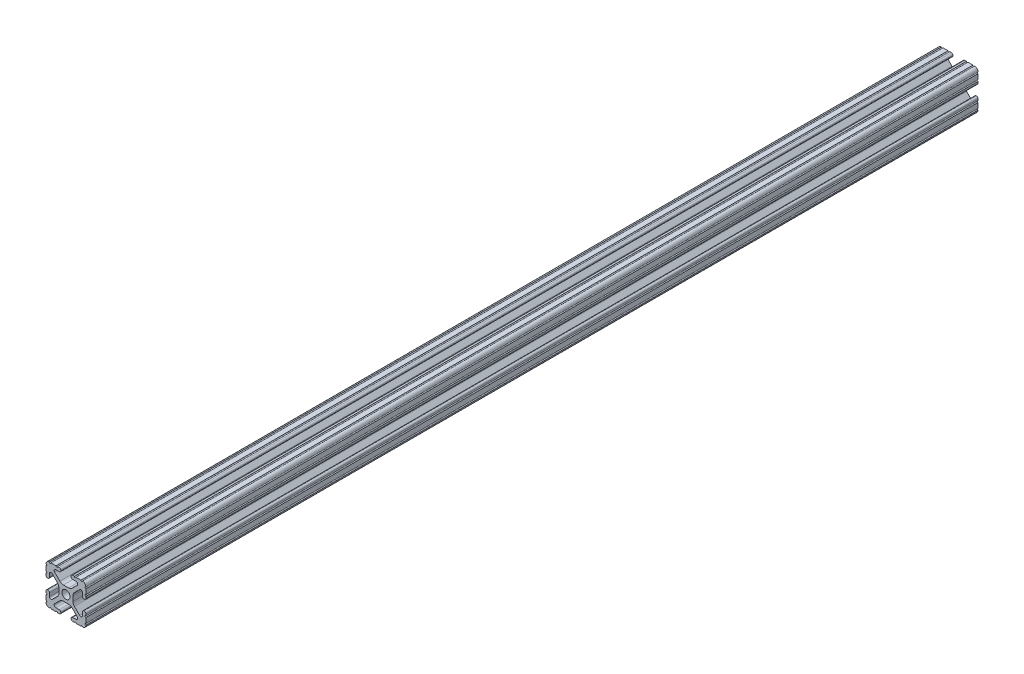
SolidWorks part; units mm, degrees
material "6061 Alloy"
ref_plane "Front" through (0, 0, 0) normal (0, 0, 1) x (1, 0, 0)
ref_plane "Top" through (0, 0, 0) normal (0, 1, 0) x (1, 0, 0)
ref_plane "Right" through (0, 0, 0) normal (1, 0, 0) x (0, 0, -1)
sketch "Sketch1" plane through (0, 0, 0) normal (0, 0, 1) x (1, 0, 0)
  line L0 (-3.2512, 12.7) -> (-3.2512, -12.7) construction
  line L1 (-12.7, -12.7) -> (12.7, -12.7) construction
  line L2 (-12.7, -12.7) -> (-12.7, 12.7) construction
  line L3 (-12.7, 12.7) -> (12.7, 12.7) construction
  line L4 (12.7, -12.7) -> (12.7, 12.7) construction
  line L5 (0, 12.7) -> (0, -12.7) construction
  line L6 (-12.7, 0) -> (12.7, 0) construction
  line L7 (3.2512, 12.7) -> (3.2512, -12.7) construction
  line L8 (-3.2512, 12.7) -> (3.2512, -12.7) construction
  circle A0 centre (0, 0) radius 2.6035
  point P0 (0, 0)
  line B0 (-7.5107, 9.4563) -> (7.5107, 9.4563) construction
  line B1 (-7.4968, -9.4098) -> (7.4968, -9.4098) construction
  line B2 (-7.1797, -8.6452) -> (-3.9523, -5.4237)
  line B3 (-1.7093, -4.4958) -> (1.7093, -4.4958)
  line B4 (3.9523, -5.4237) -> (7.1797, -8.6452)
  line B5 (6.4164, -10.4902) -> (4.2875, -10.4902)
  line B6 (3.2385, -11.5392) -> (3.2385, -11.651)
  line B7 (4.2875, -12.7) -> (5.3171, -12.7)
  line B8 (6.3331, -12.7) -> (9.5504, -12.7)
  line B9 (12.7, -9.5504) -> (12.7, -6.3331)
  line B10 (12.7, -5.3171) -> (12.7, -4.2875)
  line B11 (11.651, -3.2385) -> (11.5392, -3.2385)
  line B12 (10.4902, -4.2875) -> (10.4902, -6.4021)
  line B13 (8.7371, -7.1294) -> (5.441, -3.8408)
  line B14 (4.5085, -1.5932) -> (4.5085, 1.5932)
  line B15 (5.441, 3.8408) -> (8.7371, 7.1294)
  line B16 (10.4902, 6.4021) -> (10.4902, 4.2875)
  line B17 (11.5392, 3.2385) -> (11.651, 3.2385)
  line B18 (12.7, 4.2875) -> (12.7, 5.3171)
  line B19 (12.7, 6.3331) -> (12.7, 9.5504)
  line B20 (9.5504, 12.7) -> (6.3331, 12.7)
  line B21 (5.3171, 12.7) -> (4.2875, 12.7)
  line B22 (3.2385, 11.651) -> (3.2385, 11.5392)
  line B23 (4.2875, 10.4902) -> (6.4768, 10.4902)
  line B24 (7.207, 8.7244) -> (3.8983, 5.4232)
  line B25 (1.6558, 4.4958) -> (-1.6558, 4.4958)
  line B26 (-3.8983, 5.4232) -> (-7.207, 8.7244)
  line B27 (-6.4768, 10.4902) -> (-4.2875, 10.4902)
  line B28 (-3.2385, 11.5392) -> (-3.2385, 11.651)
  line B29 (-4.2875, 12.7) -> (-5.3171, 12.7)
  line B30 (-6.3331, 12.7) -> (-9.5504, 12.7)
  line B31 (-12.7, 9.5504) -> (-12.7, 6.3331)
  line B32 (-12.7, 5.3171) -> (-12.7, 4.2875)
  line B33 (-11.651, 3.2385) -> (-11.5392, 3.2385)
  line B34 (-10.4902, 4.2875) -> (-10.4902, 6.4021)
  line B35 (-8.7371, 7.1294) -> (-5.441, 3.8408)
  line B36 (-4.5085, 1.5932) -> (-4.5085, -1.5932)
  line B37 (-5.441, -3.8408) -> (-8.7371, -7.1294)
  line B38 (-10.4902, -6.4021) -> (-10.4902, -4.2875)
  line B39 (-11.5392, -3.2385) -> (-11.651, -3.2385)
  line B40 (-12.7, -4.2875) -> (-12.7, -5.3171)
  line B41 (-12.7, -6.3331) -> (-12.7, -9.5504)
  line B42 (-9.5504, -12.7) -> (-6.3331, -12.7)
  line B43 (-5.3171, -12.7) -> (-4.2875, -12.7)
  line B44 (-3.2385, -11.651) -> (-3.2385, -11.5392)
  line B45 (-4.2875, -10.4902) -> (-6.4164, -10.4902)
  circle B46 centre (0, 0) radius 2.6035
  arc B47 (-7.1797, -8.6452) -> (-6.4164, -10.4902) centre (-6.4164, -9.4098) ccw
  arc B48 (-1.7093, -4.4958) -> (-3.9523, -5.4237) centre (-1.7093, -7.6708) ccw
  arc B49 (3.9523, -5.4237) -> (1.7093, -4.4958) centre (1.7093, -7.6708) ccw
  arc B50 (6.4164, -10.4902) -> (7.1797, -8.6452) centre (6.4164, -9.4098) ccw
  arc B51 (4.2875, -10.4902) -> (3.2385, -11.5392) centre (4.2875, -11.5392) ccw
  arc B52 (3.2385, -11.651) -> (4.2875, -12.7) centre (4.2875, -11.651) ccw
  arc B53 (6.3331, -12.7) -> (5.3171, -12.7) centre (5.8251, -12.7) ccw
  arc B54 (10.5664, -12.6998) -> (9.5504, -12.7) centre (10.0584, -12.7) ccw
  arc B55 (10.5664, -12.6998) -> (12.6998, -10.5664) centre (10.5918, -10.5918) ccw
  arc B56 (12.7, -9.5504) -> (12.6998, -10.5664) centre (12.7, -10.0584) ccw
  arc B57 (12.7, -5.3171) -> (12.7, -6.3331) centre (12.7, -5.8251) ccw
  arc B58 (12.7, -4.2875) -> (11.651, -3.2385) centre (11.651, -4.2875) ccw
  arc B59 (11.5392, -3.2385) -> (10.4902, -4.2875) centre (11.5392, -4.2875) ccw
  arc B60 (8.7371, -7.1294) -> (10.4902, -6.4021) centre (9.4628, -6.4021) ccw
  arc B61 (4.5085, -1.5932) -> (5.441, -3.8408) centre (7.6835, -1.5932) ccw
  arc B62 (5.441, 3.8408) -> (4.5085, 1.5932) centre (7.6835, 1.5932) ccw
  arc B63 (10.4902, 6.4021) -> (8.7371, 7.1294) centre (9.4628, 6.4021) ccw
  arc B64 (10.4902, 4.2875) -> (11.5392, 3.2385) centre (11.5392, 4.2875) ccw
  arc B65 (11.651, 3.2385) -> (12.7, 4.2875) centre (11.651, 4.2875) ccw
  arc B66 (12.7, 6.3331) -> (12.7, 5.3171) centre (12.7, 5.8251) ccw
  arc B67 (12.6998, 10.5664) -> (12.7, 9.5504) centre (12.7, 10.0584) ccw
  arc B68 (12.6998, 10.5664) -> (10.5664, 12.6998) centre (10.5918, 10.5918) ccw
  arc B69 (9.5504, 12.7) -> (10.5664, 12.6998) centre (10.0584, 12.7) ccw
  arc B70 (5.3171, 12.7) -> (6.3331, 12.7) centre (5.8251, 12.7) ccw
  arc B71 (4.2875, 12.7) -> (3.2385, 11.651) centre (4.2875, 11.651) ccw
  arc B72 (3.2385, 11.5392) -> (4.2875, 10.4902) centre (4.2875, 11.5392) ccw
  arc B73 (7.207, 8.7244) -> (6.4768, 10.4902) centre (6.4768, 9.4563) ccw
  arc B74 (1.6558, 4.4958) -> (3.8983, 5.4232) centre (1.6558, 7.6708) ccw
  arc B75 (-3.8983, 5.4232) -> (-1.6558, 4.4958) centre (-1.6558, 7.6708) ccw
  arc B76 (-6.4768, 10.4902) -> (-7.207, 8.7244) centre (-6.4768, 9.4563) ccw
  arc B77 (-4.2875, 10.4902) -> (-3.2385, 11.5392) centre (-4.2875, 11.5392) ccw
  arc B78 (-3.2385, 11.651) -> (-4.2875, 12.7) centre (-4.2875, 11.651) ccw
  arc B79 (-6.3331, 12.7) -> (-5.3171, 12.7) centre (-5.8251, 12.7) ccw
  arc B80 (-10.5664, 12.6998) -> (-9.5504, 12.7) centre (-10.0584, 12.7) ccw
  arc B81 (-10.5664, 12.6998) -> (-12.6998, 10.5664) centre (-10.5918, 10.5918) ccw
  arc B82 (-12.7, 9.5504) -> (-12.6998, 10.5664) centre (-12.7, 10.0584) ccw
  arc B83 (-12.7, 5.3171) -> (-12.7, 6.3331) centre (-12.7, 5.8251) ccw
  arc B84 (-12.7, 4.2875) -> (-11.651, 3.2385) centre (-11.651, 4.2875) ccw
  arc B85 (-11.5392, 3.2385) -> (-10.4902, 4.2875) centre (-11.5392, 4.2875) ccw
  arc B86 (-8.7371, 7.1294) -> (-10.4902, 6.4021) centre (-9.4628, 6.4021) ccw
  arc B87 (-4.5085, 1.5932) -> (-5.441, 3.8408) centre (-7.6835, 1.5932) ccw
  arc B88 (-5.441, -3.8408) -> (-4.5085, -1.5932) centre (-7.6835, -1.5932) ccw
  arc B89 (-10.4902, -6.4021) -> (-8.7371, -7.1294) centre (-9.4628, -6.4021) ccw
  arc B90 (-10.4902, -4.2875) -> (-11.5392, -3.2385) centre (-11.5392, -4.2875) ccw
  arc B91 (-11.651, -3.2385) -> (-12.7, -4.2875) centre (-11.651, -4.2875) ccw
  arc B92 (-12.7, -6.3331) -> (-12.7, -5.3171) centre (-12.7, -5.8251) ccw
  arc B93 (-12.6998, -10.5664) -> (-12.7, -9.5504) centre (-12.7, -10.0584) ccw
  arc B94 (-12.6998, -10.5664) -> (-10.5664, -12.6998) centre (-10.5918, -10.5918) ccw
  arc B95 (-9.5504, -12.7) -> (-10.5664, -12.6998) centre (-10.0584, -12.7) ccw
  arc B96 (-5.3171, -12.7) -> (-6.3331, -12.7) centre (-5.8251, -12.7) ccw
  arc B97 (-4.2875, -12.7) -> (-3.2385, -11.651) centre (-4.2875, -11.651) ccw
  arc B98 (-3.2385, -11.5392) -> (-4.2875, -10.4902) centre (-4.2875, -11.5392) ccw
  dimension "Center Hole Diameter" = 5.207
  dimension "Rail Width" = 25.4
  dimension "Rail Height" = 25.4
  dimension "T-Slot Width" = 6.5024
sketch_block_instance "Block1-1"
sketch_block "Block1"
sketch "Sketch2" plane through (0, 0, 0) normal (1, 0, 0) x (0, 0, -1)
  line L0 (-284.1506, 0) -> (284.1506, 0) construction
  line L1 (0, 0) -> (0, 12.7) construction
  line L2 (12.7, 12.7) -> (-12.7, 12.7) construction
  line L3 (-3048, -12.7) -> (3048, -12.7) construction
  line L4 (-170.4904, 0) -> (0, 12.7) construction
  line L5 (0, 12.7) -> (170.4904, 0) construction
  point P5 (-170.4904, 0)
  point P9 (0, 12.7)
  point P12 (170.4904, 0)
  dimension "Length Range [Min]" = 25.4
  dimension "Rep Length" = 568.3013
  dimension "Length Range [Max]" = 6096
  dimension "D1" = 340.9808
sketch "Sketch3" plane through (0, 0, 0) normal (0, 0, 1) x (1, 0, 0)
  line L0 (-7.1797, -8.6452) -> (-3.9523, -5.4237) construction
  line L1 (-4.2875, -10.4902) -> (-6.4164, -10.4902) construction
  line L2 (-3.2385, -11.651) -> (-3.2385, -11.5392) construction
  line L3 (-5.3171, -12.7) -> (-4.2875, -12.7) construction
  line L4 (-9.5504, -12.7) -> (-6.3331, -12.7) construction
  line L5 (-12.7, -6.3331) -> (-12.7, -9.5504) construction
  line L6 (-12.7, -4.2875) -> (-12.7, -5.3171) construction
  line L7 (-11.5392, -3.2385) -> (-11.651, -3.2385) construction
  line L8 (-10.4902, -6.4021) -> (-10.4902, -4.2875) construction
  line L9 (-5.441, -3.8408) -> (-8.7371, -7.1294) construction
  line L10 (-4.5085, 1.5932) -> (-4.5085, -1.5932) construction
  line L11 (-8.7371, 7.1294) -> (-5.441, 3.8408) construction
  line L12 (-10.4902, 4.2875) -> (-10.4902, 6.4021) construction
  line L13 (-11.651, 3.2385) -> (-11.5392, 3.2385) construction
  line L14 (-12.7, 5.3171) -> (-12.7, 4.2875) construction
  line L15 (-12.7, 9.5504) -> (-12.7, 6.3331) construction
  line L16 (-6.3331, 12.7) -> (-9.5504, 12.7) construction
  line L17 (-4.2875, 12.7) -> (-5.3171, 12.7) construction
  line L18 (-3.2385, 11.5392) -> (-3.2385, 11.651) construction
  line L19 (-6.4768, 10.4902) -> (-4.2875, 10.4902) construction
  line L20 (-3.8983, 5.4232) -> (-7.207, 8.7244) construction
  line L21 (1.6558, 4.4958) -> (-1.6558, 4.4958) construction
  line L22 (7.207, 8.7244) -> (3.8983, 5.4232) construction
  line L23 (4.2875, 10.4902) -> (6.4768, 10.4902) construction
  line L24 (3.2385, 11.651) -> (3.2385, 11.5392) construction
  line L25 (5.3171, 12.7) -> (4.2875, 12.7) construction
  line L26 (9.5504, 12.7) -> (6.3331, 12.7) construction
  line L27 (12.7, 6.3331) -> (12.7, 9.5504) construction
  line L28 (12.7, 4.2875) -> (12.7, 5.3171) construction
  line L29 (11.5392, 3.2385) -> (11.651, 3.2385) construction
  line L30 (10.4902, 6.4021) -> (10.4902, 4.2875) construction
  line L31 (5.441, 3.8408) -> (8.7371, 7.1294) construction
  line L32 (4.5085, -1.5932) -> (4.5085, 1.5932) construction
  line L33 (8.7371, -7.1294) -> (5.441, -3.8408) construction
  line L34 (10.4902, -4.2875) -> (10.4902, -6.4021) construction
  line L35 (11.651, -3.2385) -> (11.5392, -3.2385) construction
  line L36 (12.7, -5.3171) -> (12.7, -4.2875) construction
  line L37 (12.7, -9.5504) -> (12.7, -6.3331) construction
  line L38 (6.3331, -12.7) -> (9.5504, -12.7) construction
  line L39 (4.2875, -12.7) -> (5.3171, -12.7) construction
  line L40 (3.2385, -11.5392) -> (3.2385, -11.651) construction
  line L41 (6.4164, -10.4902) -> (4.2875, -10.4902) construction
  line L42 (3.9523, -5.4237) -> (7.1797, -8.6452) construction
  line L43 (-1.7093, -4.4958) -> (1.7093, -4.4958) construction
  line L44 (-7.1797, -8.6452) -> (-3.9523, -5.4237)
  line L45 (-4.2875, -10.4902) -> (-6.4164, -10.4902)
  line L46 (-3.2385, -11.651) -> (-3.2385, -11.5392)
  line L47 (-5.3171, -12.7) -> (-4.2875, -12.7)
  line L48 (-9.5504, -12.7) -> (-6.3331, -12.7)
  line L49 (-12.7, -6.3331) -> (-12.7, -9.5504)
  line L50 (-12.7, -4.2875) -> (-12.7, -5.3171)
  line L51 (-11.5392, -3.2385) -> (-11.651, -3.2385)
  line L52 (-10.4902, -6.4021) -> (-10.4902, -4.2875)
  line L53 (-5.441, -3.8408) -> (-8.7371, -7.1294)
  line L54 (-4.5085, 1.5932) -> (-4.5085, -1.5932)
  line L55 (-8.7371, 7.1294) -> (-5.441, 3.8408)
  line L56 (-10.4902, 4.2875) -> (-10.4902, 6.4021)
  line L57 (-11.651, 3.2385) -> (-11.5392, 3.2385)
  line L58 (-12.7, 5.3171) -> (-12.7, 4.2875)
  line L59 (-12.7, 9.5504) -> (-12.7, 6.3331)
  line L60 (-6.3331, 12.7) -> (-9.5504, 12.7)
  line L61 (-4.2875, 12.7) -> (-5.3171, 12.7)
  line L62 (-3.2385, 11.5392) -> (-3.2385, 11.651)
  line L63 (-6.4768, 10.4902) -> (-4.2875, 10.4902)
  line L64 (-3.8983, 5.4232) -> (-7.207, 8.7244)
  line L65 (1.6558, 4.4958) -> (-1.6558, 4.4958)
  line L66 (7.207, 8.7244) -> (3.8983, 5.4232)
  line L67 (4.2875, 10.4902) -> (6.4768, 10.4902)
  line L68 (3.2385, 11.651) -> (3.2385, 11.5392)
  line L69 (5.3171, 12.7) -> (4.2875, 12.7)
  line L70 (9.5504, 12.7) -> (6.3331, 12.7)
  line L71 (12.7, 6.3331) -> (12.7, 9.5504)
  line L72 (12.7, 4.2875) -> (12.7, 5.3171)
  line L73 (11.5392, 3.2385) -> (11.651, 3.2385)
  line L74 (10.4902, 6.4021) -> (10.4902, 4.2875)
  line L75 (5.441, 3.8408) -> (8.7371, 7.1294)
  line L76 (4.5085, -1.5932) -> (4.5085, 1.5932)
  line L77 (8.7371, -7.1294) -> (5.441, -3.8408)
  line L78 (10.4902, -4.2875) -> (10.4902, -6.4021)
  line L79 (11.651, -3.2385) -> (11.5392, -3.2385)
  line L80 (12.7, -5.3171) -> (12.7, -4.2875)
  line L81 (12.7, -9.5504) -> (12.7, -6.3331)
  line L82 (6.3331, -12.7) -> (9.5504, -12.7)
  line L83 (4.2875, -12.7) -> (5.3171, -12.7)
  line L84 (3.2385, -11.5392) -> (3.2385, -11.651)
  line L85 (6.4164, -10.4902) -> (4.2875, -10.4902)
  line L86 (3.9523, -5.4237) -> (7.1797, -8.6452)
  line L87 (-1.7093, -4.4958) -> (1.7093, -4.4958)
  circle A0 centre (0, 0) radius 2.6035 construction
  circle A1 centre (0, 0) radius 2.6035
  circle A2 centre (0, 0) radius 2.6035
  arc A3 (-1.7093, -4.4958) -> (-3.9523, -5.4237) centre (-1.7093, -7.6708) ccw construction
  arc A4 (-7.1797, -8.6452) -> (-6.4164, -10.4902) centre (-6.4164, -9.4098) ccw construction
  arc A5 (-3.2385, -11.5392) -> (-4.2875, -10.4902) centre (-4.2875, -11.5392) ccw construction
  arc A6 (-4.2875, -12.7) -> (-3.2385, -11.651) centre (-4.2875, -11.651) ccw construction
  arc A7 (-5.3171, -12.7) -> (-6.3331, -12.7) centre (-5.8251, -12.7) ccw construction
  arc A8 (-9.5504, -12.7) -> (-10.5664, -12.6998) centre (-10.0584, -12.7) ccw construction
  arc A9 (-12.6998, -10.5664) -> (-10.5664, -12.6998) centre (-10.5918, -10.5918) ccw construction
  arc A10 (-12.6998, -10.5664) -> (-12.7, -9.5504) centre (-12.7, -10.0584) ccw construction
  arc A11 (-12.7, -6.3331) -> (-12.7, -5.3171) centre (-12.7, -5.8251) ccw construction
  arc A12 (-11.651, -3.2385) -> (-12.7, -4.2875) centre (-11.651, -4.2875) ccw construction
  arc A13 (-10.4902, -4.2875) -> (-11.5392, -3.2385) centre (-11.5392, -4.2875) ccw construction
  arc A14 (-10.4902, -6.4021) -> (-8.7371, -7.1294) centre (-9.4628, -6.4021) ccw construction
  arc A15 (-5.441, -3.8408) -> (-4.5085, -1.5932) centre (-7.6835, -1.5932) ccw construction
  arc A16 (-4.5085, 1.5932) -> (-5.441, 3.8408) centre (-7.6835, 1.5932) ccw construction
  arc A17 (-8.7371, 7.1294) -> (-10.4902, 6.4021) centre (-9.4628, 6.4021) ccw construction
  arc A18 (-11.5392, 3.2385) -> (-10.4902, 4.2875) centre (-11.5392, 4.2875) ccw construction
  arc A19 (-12.7, 4.2875) -> (-11.651, 3.2385) centre (-11.651, 4.2875) ccw construction
  arc A20 (-12.7, 5.3171) -> (-12.7, 6.3331) centre (-12.7, 5.8251) ccw construction
  arc A21 (-12.7, 9.5504) -> (-12.6998, 10.5664) centre (-12.7, 10.0584) ccw construction
  arc A22 (-10.5664, 12.6998) -> (-12.6998, 10.5664) centre (-10.5918, 10.5918) ccw construction
  arc A23 (-10.5664, 12.6998) -> (-9.5504, 12.7) centre (-10.0584, 12.7) ccw construction
  arc A24 (-6.3331, 12.7) -> (-5.3171, 12.7) centre (-5.8251, 12.7) ccw construction
  arc A25 (-3.2385, 11.651) -> (-4.2875, 12.7) centre (-4.2875, 11.651) ccw construction
  arc A26 (-4.2875, 10.4902) -> (-3.2385, 11.5392) centre (-4.2875, 11.5392) ccw construction
  arc A27 (-6.4768, 10.4902) -> (-7.207, 8.7244) centre (-6.4768, 9.4563) ccw construction
  arc A28 (-3.8983, 5.4232) -> (-1.6558, 4.4958) centre (-1.6558, 7.6708) ccw construction
  arc A29 (1.6558, 4.4958) -> (3.8983, 5.4232) centre (1.6558, 7.6708) ccw construction
  arc A30 (7.207, 8.7244) -> (6.4768, 10.4902) centre (6.4768, 9.4563) ccw construction
  arc A31 (3.2385, 11.5392) -> (4.2875, 10.4902) centre (4.2875, 11.5392) ccw construction
  arc A32 (4.2875, 12.7) -> (3.2385, 11.651) centre (4.2875, 11.651) ccw construction
  arc A33 (5.3171, 12.7) -> (6.3331, 12.7) centre (5.8251, 12.7) ccw construction
  arc A34 (9.5504, 12.7) -> (10.5664, 12.6998) centre (10.0584, 12.7) ccw construction
  arc A35 (12.6998, 10.5664) -> (10.5664, 12.6998) centre (10.5918, 10.5918) ccw construction
  arc A36 (12.6998, 10.5664) -> (12.7, 9.5504) centre (12.7, 10.0584) ccw construction
  arc A37 (12.7, 6.3331) -> (12.7, 5.3171) centre (12.7, 5.8251) ccw construction
  arc A38 (11.651, 3.2385) -> (12.7, 4.2875) centre (11.651, 4.2875) ccw construction
  arc A39 (10.4902, 4.2875) -> (11.5392, 3.2385) centre (11.5392, 4.2875) ccw construction
  arc A40 (10.4902, 6.4021) -> (8.7371, 7.1294) centre (9.4628, 6.4021) ccw construction
  arc A41 (5.441, 3.8408) -> (4.5085, 1.5932) centre (7.6835, 1.5932) ccw construction
  arc A42 (4.5085, -1.5932) -> (5.441, -3.8408) centre (7.6835, -1.5932) ccw construction
  arc A43 (8.7371, -7.1294) -> (10.4902, -6.4021) centre (9.4628, -6.4021) ccw construction
  arc A44 (11.5392, -3.2385) -> (10.4902, -4.2875) centre (11.5392, -4.2875) ccw construction
  arc A45 (12.7, -4.2875) -> (11.651, -3.2385) centre (11.651, -4.2875) ccw construction
  arc A46 (12.7, -5.3171) -> (12.7, -6.3331) centre (12.7, -5.8251) ccw construction
  arc A47 (12.7, -9.5504) -> (12.6998, -10.5664) centre (12.7, -10.0584) ccw construction
  arc A48 (10.5664, -12.6998) -> (12.6998, -10.5664) centre (10.5918, -10.5918) ccw construction
  arc A49 (10.5664, -12.6998) -> (9.5504, -12.7) centre (10.0584, -12.7) ccw construction
  arc A50 (6.3331, -12.7) -> (5.3171, -12.7) centre (5.8251, -12.7) ccw construction
  arc A51 (3.2385, -11.651) -> (4.2875, -12.7) centre (4.2875, -11.651) ccw construction
  arc A52 (4.2875, -10.4902) -> (3.2385, -11.5392) centre (4.2875, -11.5392) ccw construction
  arc A53 (6.4164, -10.4902) -> (7.1797, -8.6452) centre (6.4164, -9.4098) ccw construction
  arc A54 (3.9523, -5.4237) -> (1.7093, -4.4958) centre (1.7093, -7.6708) ccw construction
  circle A55 centre (0, 0) radius 2.6035
  arc A56 (-1.7093, -4.4958) -> (-3.9523, -5.4237) centre (-1.7093, -7.6708) ccw
  arc A57 (-7.1797, -8.6452) -> (-6.4164, -10.4902) centre (-6.4164, -9.4098) ccw
  arc A58 (-3.2385, -11.5392) -> (-4.2875, -10.4902) centre (-4.2875, -11.5392) ccw
  arc A59 (-4.2875, -12.7) -> (-3.2385, -11.651) centre (-4.2875, -11.651) ccw
  arc A60 (-5.3171, -12.7) -> (-6.3331, -12.7) centre (-5.8251, -12.7) ccw
  arc A61 (-9.5504, -12.7) -> (-10.5664, -12.6998) centre (-10.0584, -12.7) ccw
  arc A62 (-12.6998, -10.5664) -> (-10.5664, -12.6998) centre (-10.5918, -10.5918) ccw
  arc A63 (-12.6998, -10.5664) -> (-12.7, -9.5504) centre (-12.7, -10.0584) ccw
  arc A64 (-12.7, -6.3331) -> (-12.7, -5.3171) centre (-12.7, -5.8251) ccw
  arc A65 (-11.651, -3.2385) -> (-12.7, -4.2875) centre (-11.651, -4.2875) ccw
  arc A66 (-10.4902, -4.2875) -> (-11.5392, -3.2385) centre (-11.5392, -4.2875) ccw
  arc A67 (-10.4902, -6.4021) -> (-8.7371, -7.1294) centre (-9.4628, -6.4021) ccw
  arc A68 (-5.441, -3.8408) -> (-4.5085, -1.5932) centre (-7.6835, -1.5932) ccw
  arc A69 (-4.5085, 1.5932) -> (-5.441, 3.8408) centre (-7.6835, 1.5932) ccw
  arc A70 (-8.7371, 7.1294) -> (-10.4902, 6.4021) centre (-9.4628, 6.4021) ccw
  arc A71 (-11.5392, 3.2385) -> (-10.4902, 4.2875) centre (-11.5392, 4.2875) ccw
  arc A72 (-12.7, 4.2875) -> (-11.651, 3.2385) centre (-11.651, 4.2875) ccw
  arc A73 (-12.7, 5.3171) -> (-12.7, 6.3331) centre (-12.7, 5.8251) ccw
  arc A74 (-12.7, 9.5504) -> (-12.6998, 10.5664) centre (-12.7, 10.0584) ccw
  arc A75 (-10.5664, 12.6998) -> (-12.6998, 10.5664) centre (-10.5918, 10.5918) ccw
  arc A76 (-10.5664, 12.6998) -> (-9.5504, 12.7) centre (-10.0584, 12.7) ccw
  arc A77 (-6.3331, 12.7) -> (-5.3171, 12.7) centre (-5.8251, 12.7) ccw
  arc A78 (-3.2385, 11.651) -> (-4.2875, 12.7) centre (-4.2875, 11.651) ccw
  arc A79 (-4.2875, 10.4902) -> (-3.2385, 11.5392) centre (-4.2875, 11.5392) ccw
  arc A80 (-6.4768, 10.4902) -> (-7.207, 8.7244) centre (-6.4768, 9.4563) ccw
  arc A81 (-3.8983, 5.4232) -> (-1.6558, 4.4958) centre (-1.6558, 7.6708) ccw
  arc A82 (1.6558, 4.4958) -> (3.8983, 5.4232) centre (1.6558, 7.6708) ccw
  arc A83 (7.207, 8.7244) -> (6.4768, 10.4902) centre (6.4768, 9.4563) ccw
  arc A84 (3.2385, 11.5392) -> (4.2875, 10.4902) centre (4.2875, 11.5392) ccw
  arc A85 (4.2875, 12.7) -> (3.2385, 11.651) centre (4.2875, 11.651) ccw
  arc A86 (5.3171, 12.7) -> (6.3331, 12.7) centre (5.8251, 12.7) ccw
  arc A87 (9.5504, 12.7) -> (10.5664, 12.6998) centre (10.0584, 12.7) ccw
  arc A88 (12.6998, 10.5664) -> (10.5664, 12.6998) centre (10.5918, 10.5918) ccw
  arc A89 (12.6998, 10.5664) -> (12.7, 9.5504) centre (12.7, 10.0584) ccw
  arc A90 (12.7, 6.3331) -> (12.7, 5.3171) centre (12.7, 5.8251) ccw
  arc A91 (11.651, 3.2385) -> (12.7, 4.2875) centre (11.651, 4.2875) ccw
  arc A92 (10.4902, 4.2875) -> (11.5392, 3.2385) centre (11.5392, 4.2875) ccw
  arc A93 (10.4902, 6.4021) -> (8.7371, 7.1294) centre (9.4628, 6.4021) ccw
  arc A94 (5.441, 3.8408) -> (4.5085, 1.5932) centre (7.6835, 1.5932) ccw
  arc A95 (4.5085, -1.5932) -> (5.441, -3.8408) centre (7.6835, -1.5932) ccw
  arc A96 (8.7371, -7.1294) -> (10.4902, -6.4021) centre (9.4628, -6.4021) ccw
  arc A97 (11.5392, -3.2385) -> (10.4902, -4.2875) centre (11.5392, -4.2875) ccw
  arc A98 (12.7, -4.2875) -> (11.651, -3.2385) centre (11.651, -4.2875) ccw
  arc A99 (12.7, -5.3171) -> (12.7, -6.3331) centre (12.7, -5.8251) ccw
  arc A100 (12.7, -9.5504) -> (12.6998, -10.5664) centre (12.7, -10.0584) ccw
  arc A101 (10.5664, -12.6998) -> (12.6998, -10.5664) centre (10.5918, -10.5918) ccw
  arc A102 (10.5664, -12.6998) -> (9.5504, -12.7) centre (10.0584, -12.7) ccw
  arc A103 (6.3331, -12.7) -> (5.3171, -12.7) centre (5.8251, -12.7) ccw
  arc A104 (3.2385, -11.651) -> (4.2875, -12.7) centre (4.2875, -11.651) ccw
  arc A105 (4.2875, -10.4902) -> (3.2385, -11.5392) centre (4.2875, -11.5392) ccw
  arc A106 (6.4164, -10.4902) -> (7.1797, -8.6452) centre (6.4164, -9.4098) ccw
  arc A107 (3.9523, -5.4237) -> (1.7093, -4.4958) centre (1.7093, -7.6708) ccw
  dimension "D1" = 0
extrude "Boss-Extrude1" add sketch "Sketch3" along normal up to vertex (284.1506 mm away) and the other way up to vertex (284.1506 mm away) contours A56 L44 A57 L45 A58 L46 A59 L47 A60 L48 A61 A62 A63 L49 A64 L50 A65 L51 A66 L52 A67 L53 A68 L54 A69 L55 A70 L56 A71 L57 A72 L58 A73 L59 A74 A75 A76 L60 A77 L61 A78 L62 A79 L63 A80 L64 A81 L65 A82 L66 A83 L67 A84 L68 A85 L69 A86 L70 A87 A88 A89 L71 A90 L72 A91 L73 A92 L74 A93 L75 A94 L76 A95 L77 A96 L78 A97 L79 A98 L80 A99 L81 A100 A101 A102 L82 A103 L83 A104 L84 A105 L85 A106 L86 A107 L87 | A2 up to point (0, 0, 284.1506) other way up to point (0, 0, -284.1506)
equation "\"D1@Sketch2\"=\"Rep Length@Sketch2\"*.6"
